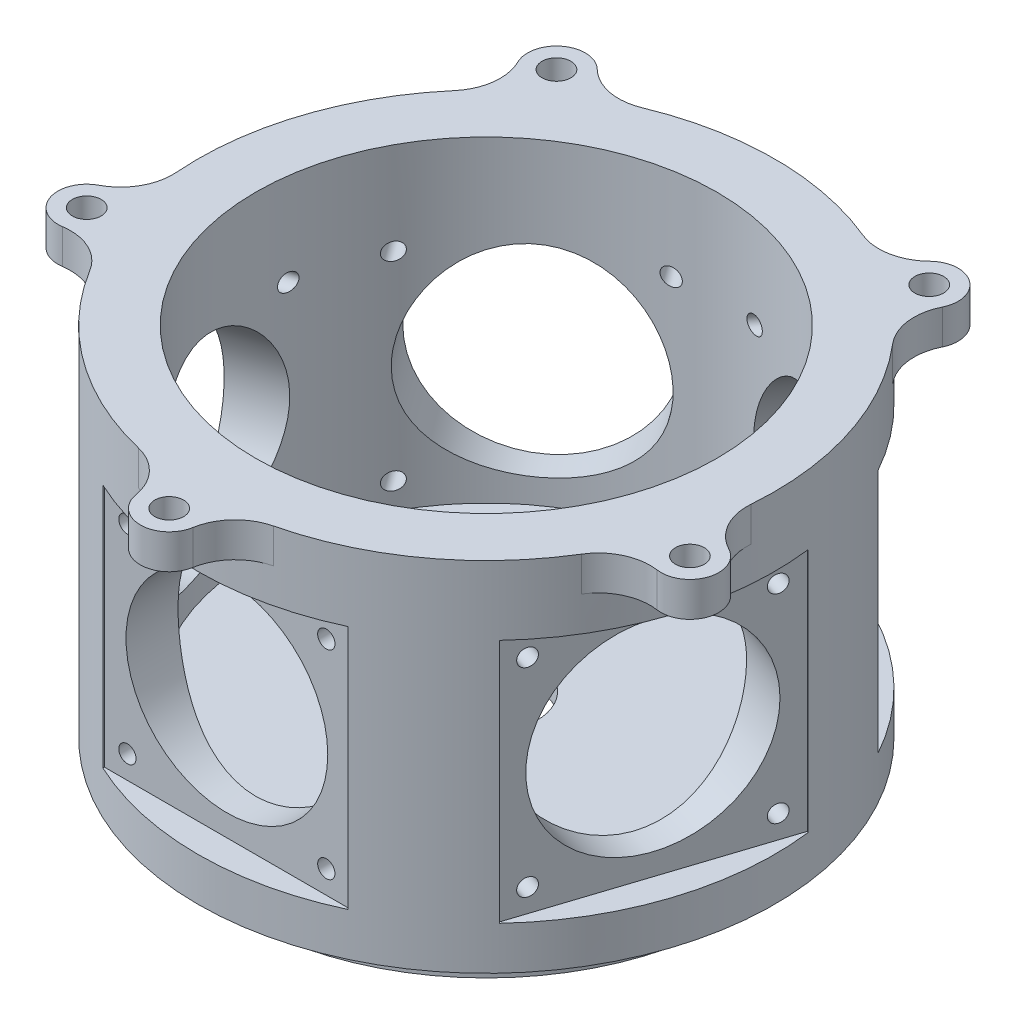
SolidWorks part; units mm, degrees
ref_plane "Front Plane" through (0, 0, 0) normal (0, 0, 1) x (1, 0, 0)
ref_plane "Top Plane" through (0, 0, 0) normal (0, 1, 0) x (1, 0, 0)
ref_plane "Right Plane" through (0, 0, 0) normal (1, 0, 0) x (0, 0, -1)
sketch "Sketch1" plane through (0, 0, 0) normal (0, 1, 0) x (1, 0, 0)
  circle A0 centre (0, 0) radius 100
  dimension "D1" = 200
extrude "Boss-Extrude1" add sketch "Sketch1" along normal blind 124
sketch "Sketch2" plane through (0, 124, 0) normal (0, 1, 0) x (1, 0, 0)
  line L0 (0, 124.8971) -> (0, -143.1836) construction
  circle A0 centre (0, 0) radius 110 construction
  circle A1 centre (0, -110) radius 5
  arc A2 (-9.9897, -109.5455) -> (9.9897, -109.5455) centre (0, -110) ccw
  arc A3 (-9.8564, -111.6883) -> (-23.3882, -97.2265) centre (-27.5981, -114.7273) ccw
  circle A4 centre (0, 0) radius 100 construction
  arc A5 (9.8564, -111.6883) -> (23.3882, -97.2265) centre (27.5981, -114.7273) cw
  circle A7 centre (0, 0) radius 100
  circle A8 centre (0, 0) radius 100
  dimension "D1" = 220
  dimension "D2" = 10
  dimension "D3" = 20
  dimension "D4" = 36
  dimension "D5" = 0
extrude "Boss-Extrude2" add sketch "Sketch2" against normal blind 12
pattern_circular "CirPattern3" count 5 over 360 about axis through (0, 0, 0) along (0, 1, 0) of "Boss-Extrude2"
sketch "Sketch3" plane through (0, 0, 0) normal (0, -1, 0) x (1, 0, 0)
  circle A0 centre (0, 0) radius 80
  dimension "D1" = 160
extrude "Extrude-Thin1" add sketch "Sketch3" along normal blind 12 thin
sketch "Sketch4" plane through (0, 0, 0) normal (0, -1, 0) x (1, 0, 0)
  circle A0 centre (0, 0) radius 80
extrude "Cut-Extrude1" cut sketch "Sketch4" against normal blind 6
ref_plane "Plane1" through (0, 0, 100) normal (0, 0, 1) x (1, 0, 0)
sketch "Sketch5" plane through (0, 0, 100) normal (0, 0, 1) x (1, 0, 0)
  line L0 (0, 155.7395) -> (0, -59.1255) construction
  line L1 (-170.3264, 56) -> (179.504, 56) construction
  line L4 (121, 0) -> (-121, 0) construction
  line L5 (-42.5, 15) -> (42.5, 15)
  line L6 (-42.5, 15) -> (-42.5, 100)
  line L7 (-42.5, 100) -> (42.5, 100)
  line L8 (42.5, 15) -> (42.5, 100)
  point P9 (0, 56)
  dimension "D3" = 15
  dimension "D1" = 85
  dimension "D2" = 85
extrude "Cut-Extrude2" cut sketch "Sketch5" against normal blind 10
sketch "Sketch9" plane through (0, 124, 0) normal (0, 1, 0) x (1, 0, 0)
  circle A0 centre (0, 0) radius 80
  dimension "D1" = 160
extrude "Cut-Extrude4" cut sketch "Sketch9" against normal blind 110
sketch "Sketch10" plane through (0, 0, 90) normal (0, 0, 1) x (1, 0, 0)
  line L0 (0, 108.5016) -> (0, -51.8374) construction
  line L1 (0, 124) -> (0, 112) construction
  line L2 (0, 14) -> (0, 124) construction
  line L3 (0, -12) -> (0, 6) construction
  line L4 (-115.5304, 57.5) -> (158.4494, 57.5) construction
  line L5 (-42.5, 100) -> (42.5, 100) construction
  line L6 (42.5, 15) -> (-42.5, 15) construction
  line L7 (-42.5, 100) -> (-42.5, 15) construction
  line L8 (42.5, 100) -> (42.5, 15) construction
  line L9 (-42.5, 15) -> (-42.5, 100) construction
  circle A0 centre (0, 57.5) radius 35
  circle A1 centre (-34.5, 92) radius 3
  circle A2 centre (34.5, 92) radius 3
  circle A3 centre (-34.5, 23) radius 3
  circle A4 centre (34.5, 23) radius 3
  dimension "D1" = 70
  dimension "D2" = 6
  dimension "D3" = 8
  dimension "D4" = 8
extrude "Cut-Extrude5" cut sketch "Sketch10" against normal up to surface (18.0625 mm away)
pattern_circular "CirPattern5" count 5 over 360 about axis through (0, 0, 0) along (0, 1, 0) of "Cut-Extrude2", "Cut-Extrude5"
sketch "Sketch11" plane through (0, 6, 0) normal (0, -1, 0) x (1, 0, 0)
  circle A0 centre (0, 0) radius 17.5
  dimension "D1" = 35
extrude "Cut-Extrude6" cut sketch "Sketch11" against normal through all
